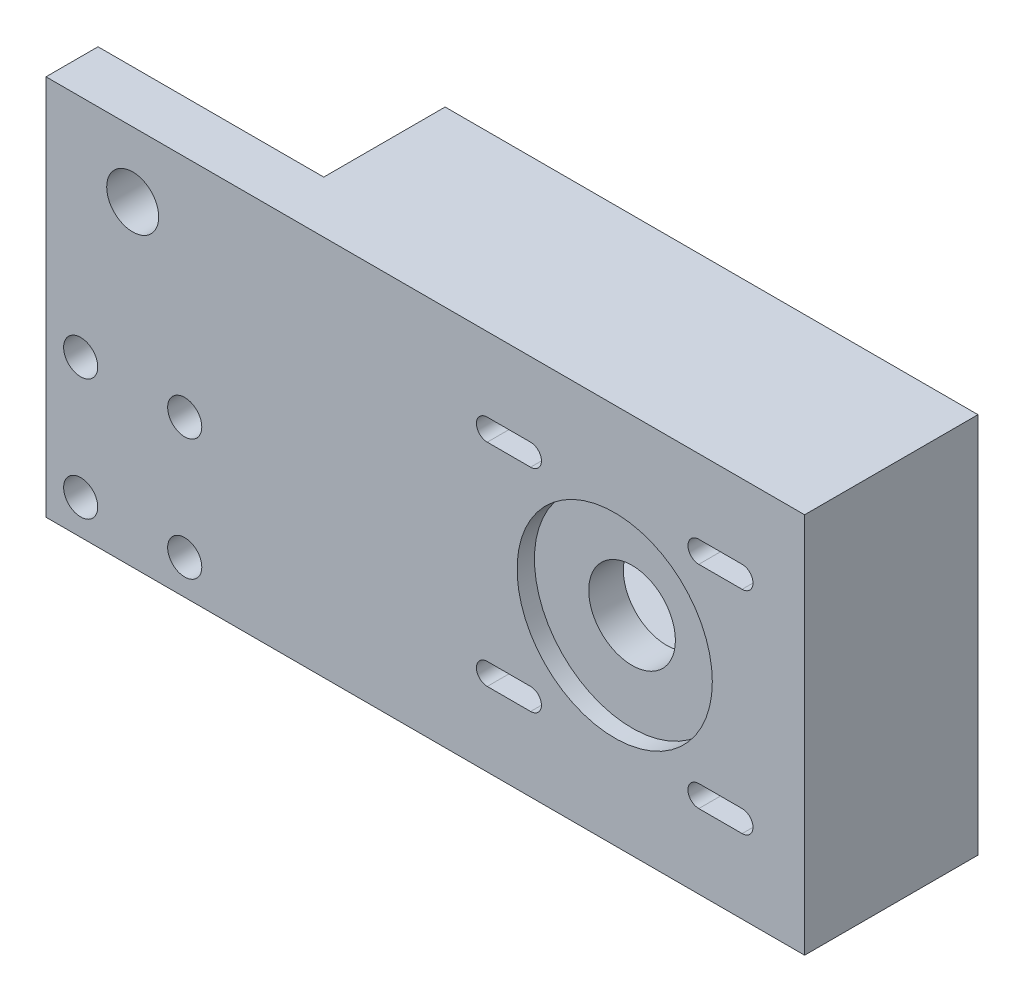
SolidWorks part; units mm, degrees
ref_plane "Front Plane" through (0, 0, 0) normal (0, 0, 1) x (1, 0, 0)
ref_plane "Top Plane" through (0, 0, 0) normal (0, 1, 0) x (1, 0, 0)
ref_plane "Right Plane" through (0, 0, 0) normal (1, 0, 0) x (0, 0, -1)
sketch "Sketch2" plane through (0, 0, 0) normal (0, 0, 1) x (1, 0, 0)
  line L0 (70.9882, 43.434) -> (64.6382, 43.434) construction
  line L1 (0, 0) -> (111.125, 0)
  line L2 (0, 0) -> (0, 55.88)
  line L3 (0, 55.88) -> (111.125, 55.88)
  line L4 (111.125, 0) -> (111.125, 55.88)
  line L5 (98.8012, 12.446) -> (67.8132, 12.446) construction
  line L6 (98.8012, 12.446) -> (98.8012, 43.434) construction
  line L7 (98.8012, 43.434) -> (67.8132, 43.434) construction
  line L8 (67.8132, 12.446) -> (67.8132, 43.434) construction
  line L9 (98.8012, 12.446) -> (67.8132, 43.434) construction
  line L10 (98.8012, 43.434) -> (67.8132, 12.446) construction
  line L11 (104.8972, 6.35) -> (61.7172, 6.35) construction
  line L12 (104.8972, 6.35) -> (104.8972, 49.53) construction
  line L13 (104.8972, 49.53) -> (61.7172, 49.53) construction
  line L14 (61.7172, 6.35) -> (61.7172, 49.53) construction
  line L15 (104.8972, 6.35) -> (61.7172, 49.53) construction
  line L16 (104.8972, 49.53) -> (61.7172, 6.35) construction
  line L17 (70.9882, 41.8465) -> (64.6382, 41.8465)
  line L18 (70.9882, 45.0215) -> (64.6382, 45.0215)
  line L19 (101.9762, 43.434) -> (95.6262, 43.434) construction
  line L20 (101.9762, 41.8465) -> (95.6262, 41.8465)
  line L21 (101.9762, 45.0215) -> (95.6262, 45.0215)
  line L22 (101.9762, 12.446) -> (95.6262, 12.446) construction
  line L23 (101.9762, 10.8585) -> (95.6262, 10.8585)
  line L24 (101.9762, 14.0335) -> (95.6262, 14.0335)
  line L25 (70.9882, 12.446) -> (64.6382, 12.446) construction
  line L26 (70.9882, 10.8585) -> (64.6382, 10.8585)
  line L27 (70.9882, 14.0335) -> (64.6382, 14.0335)
  line L28 (12.7, 46.355) -> (83.3072, 27.94) construction
  circle A0 centre (12.7, 46.355) radius 3.81
  circle A1 centre (83.3072, 27.94) radius 14.3521 construction
  arc A2 (70.9882, 41.8465) -> (70.9882, 45.0215) centre (70.9882, 43.434) ccw
  arc A3 (64.6382, 45.0215) -> (64.6382, 41.8465) centre (64.6382, 43.434) ccw
  arc A4 (101.9762, 41.8465) -> (101.9762, 45.0215) centre (101.9762, 43.434) ccw
  arc A5 (95.6262, 45.0215) -> (95.6262, 41.8465) centre (95.6262, 43.434) ccw
  arc A6 (101.9762, 10.8585) -> (101.9762, 14.0335) centre (101.9762, 12.446) ccw
  arc A7 (95.6262, 14.0335) -> (95.6262, 10.8585) centre (95.6262, 12.446) ccw
  arc A8 (70.9882, 10.8585) -> (70.9882, 14.0335) centre (70.9882, 12.446) ccw
  arc A9 (64.6382, 14.0335) -> (64.6382, 10.8585) centre (64.6382, 12.446) ccw
  point P9 (111.125, 27.94)
  point P20 (67.8132, 43.434)
  point P29 (98.8012, 43.434)
  point P36 (98.8012, 12.446)
  point P43 (67.8132, 12.446)
  dimension "D3" = 7.62
  dimension "D11" = 1.5875
  dimension "D1" = 55.88
  dimension "D2" = 111.125
  dimension "D4" = 9.525
  dimension "D5" = 12.7
  dimension "D6" = 72.9691
  dimension "D7" = 30.988
  dimension "D8" = 30.988
  dimension "D9" = 43.18
  dimension "D10" = 43.18
  dimension "D12" = 6.35
  dimension "D13" = 2
  dimension "D14" = 2
extrude "Boss-Extrude1" add sketch "Sketch2" along normal blind 25.4
ref_plane "Center Plane" through (0, 27.94, 0) normal (0, 1, 0) x (1, 0, 0)
sketch "Sketch4" plane through (0, 0, 0) normal (0, 0, -1) x (-1, 0, 0)
  circle A0 centre (-12.7, 46.355) radius 15.24
  dimension "D1" = 30.48
extrude "Cut-Extrude2" cut sketch "Sketch4" against normal blind 17.78
sketch "Sketch5" plane through (0, 0, 0) normal (0, 0, -1) x (-1, 0, 0)
  line L2 (0, 54.7792) -> (0, 55.88)
  line L3 (0, 55.88) -> (-0.8033, 55.88)
  line L4 (0, 54.7792) -> (0, 55.88)
  line L5 (0, 55.88) -> (-0.8033, 55.88)
  arc A1 (0, 54.7792) -> (-0.8033, 55.88) centre (-12.7, 46.355) ccw
  arc A2 (0, 54.7792) -> (-0.8033, 55.88) centre (-12.7, 46.355) ccw
  dimension "D1" = 0
extrude "Cut-Extrude3" cut sketch "Sketch5" against normal blind 17.78
sketch "Sketch6" plane through (0, 0, 0) normal (0, 0, -1) x (-1, 0, 0)
  circle A0 centre (-98.8012, 43.434) radius 6.35
  circle A1 centre (-98.8012, 12.446) radius 6.35
  circle A2 centre (-67.8132, 43.434) radius 6.35
  circle A3 centre (-67.8132, 12.446) radius 6.35
  dimension "D1" = 12.7
extrude "Cut-Extrude4" cut sketch "Sketch6" against normal blind 20.32
sketch "Sketch7" plane through (0, 0, 25.4) normal (0, 0, 1) x (1, 0, 0)
  circle A0 centre (83.3072, 27.94) radius 14.3002
  dimension "D1" = 28.6004
extrude "Cut-Extrude5" cut sketch "Sketch7" against normal blind 2.54
sketch "Sketch8" plane through (0, 0, 22.86) normal (0, 0, 1) x (1, 0, 0)
  circle A0 centre (83.3072, 27.94) radius 6.35
  dimension "D1" = 12.7
extrude "Cut-Extrude6" cut sketch "Sketch8" against normal through all
sketch "Sketch9" plane through (0, 0, 0) normal (0, 0, -1) x (-1, 0, 0)
  line L0 (-86.7653, 38.8343) -> (-17.3108, 60.8808)
  line L1 (-81.0041, 16.7444) -> (-9.6292, 31.4276)
  circle A0 centre (-83.3072, 27.94) radius 11.43
  circle A1 centre (-12.7, 46.355) radius 15.24
  arc A2 (-24.5967, 55.88) -> (0, 37.9308) centre (-12.7, 46.355) ccw construction
  circle M1 centre (-83.3072, 27.94) radius 6.35
  circle M3 centre (-67.8132, 43.434) radius 6.35
  arc M6 (0, 37.9308) -> (-24.5967, 55.88) centre (-12.7, 46.355) cw
  line M7 (-24.5967, 55.88) -> (-111.125, 55.88)
  dimension "D1" = 22.86
extrude "Cut-Extrude7" cut sketch "Sketch9" against normal blind 17.78 contours A0 M1 | A0 L1 L0 M6 M7 M3
sketch "Sketch10" plane through (0, 0, 25.4) normal (0, 0, 1) x (1, 0, 0)
  line L0 (0, 0) -> (0, 55.88) construction
  line L1 (0, 0) -> (111.125, 0) construction
  circle A0 centre (5.08, 5.08) radius 2.5
  circle A1 centre (20.32, 5.08) radius 2.5
  circle A2 centre (20.32, 22.86) radius 2.5
  circle A3 centre (5.08, 22.86) radius 2.5
  dimension "D1" = 5
  dimension "D2" = 5.08
  dimension "D3" = 5.08
  dimension "D4" = 2
  dimension "D5" = 2
extrude "Cut-Extrude8" cut sketch "Sketch10" against normal through all
